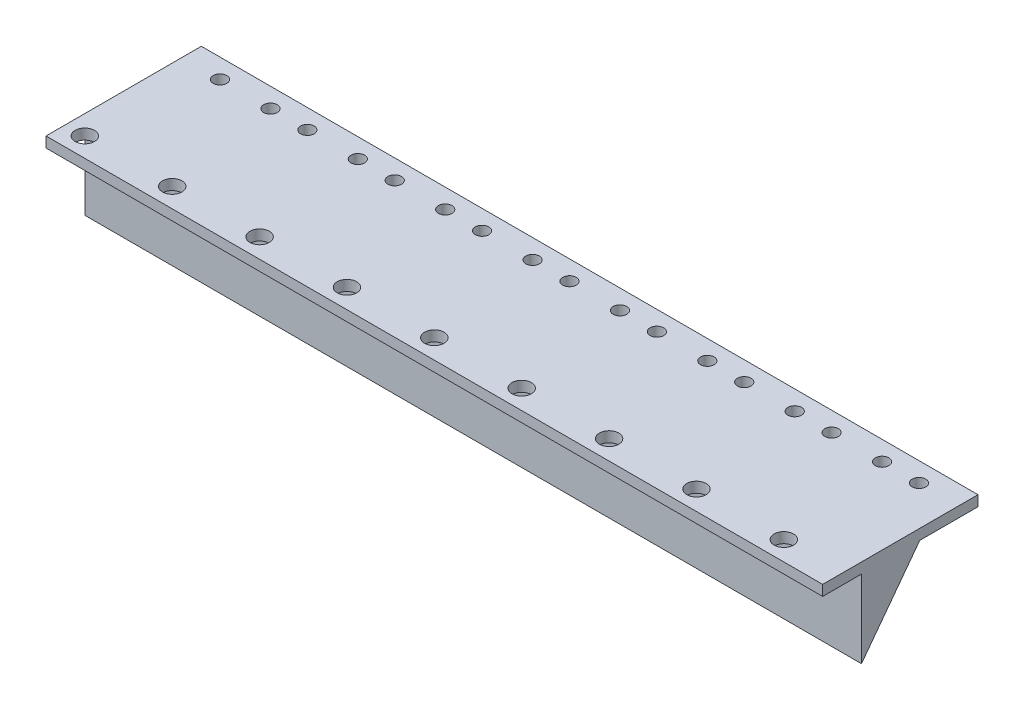
SolidWorks part; units mm, degrees
ref_plane "Front Plane" through (0, 0, 0) normal (0, 0, 1) x (1, 0, 0)
ref_plane "Top Plane" through (0, 0, 0) normal (0, 1, 0) x (1, 0, 0)
ref_plane "Right Plane" through (0, 0, 0) normal (1, 0, 0) x (0, 0, -1)
sketch "Sketch1" plane through (0, 0, 0) normal (0, 1, 0) x (1, 0, 0)
  line L1 (-100, -20) -> (100, -20)
  line L2 (-100, -20) -> (-100, 20)
  line L3 (-100, 20) -> (100, 20)
  line L4 (100, -20) -> (100, 20)
  line L5 (-100, -20) -> (100, 20) construction
  line L6 (-100, 20) -> (100, -20) construction
  point P0 (0, 0)
  dimension "D1" = 200
  dimension "D2" = 40
extrude "Boss-Extrude1" add sketch "Sketch1" along normal blind 2.7
sketch "Sketch2" plane through (0, 2.7, 0) normal (0, 1, 0) x (1, 0, 0)
  line L0 (100, 20) -> (-100, 20) construction
  line L1 (-100, 20) -> (-100, -20) construction
  circle A0 centre (-90.2, 15) radius 1.75
  dimension "D1" = 3.5
  dimension "D2" = 5
  dimension "D3" = 9.8
extrude "Cut-Extrude1" cut sketch "Sketch2" against normal through all contours A0
sketch "Sketch3" plane through (0, 2.7, 0) normal (0, 1, 0) x (1, 0, 0)
  line L0 (100, 20) -> (-100, 20) construction
  circle A0 centre (-77.2, 15) radius 1.75
  circle A1 centre (-90.2, 15) radius 1.75 construction
  dimension "D1" = 3.5
  dimension "D2" = 5
  dimension "D3" = 13
extrude "Cut-Extrude2" cut sketch "Sketch3" against normal through all
sketch "Sketch4" plane through (0, 2.7, 0) normal (0, 1, 0) x (1, 0, 0)
  line L0 (100, 20) -> (-100, 20) construction
  circle A0 centre (-67.7, 15) radius 1.75
  circle A1 centre (-77.2, 15) radius 1.75 construction
  dimension "D1" = 3.5
  dimension "D2" = 5
  dimension "D3" = 9.5
extrude "Cut-Extrude3" cut sketch "Sketch4" against normal through all
sketch "Sketch5" plane through (0, 2.7, 0) normal (0, 1, 0) x (1, 0, 0)
  line L0 (100, 20) -> (-100, 20) construction
  circle A0 centre (-54.7, 15) radius 1.75
  circle A1 centre (-67.7, 15) radius 1.75 construction
  dimension "D1" = 3.5
  dimension "D2" = 5
  dimension "D3" = 13
extrude "Cut-Extrude4" cut sketch "Sketch5" against normal through all
pattern_linear "LPattern2" count 2 spacing 9.5 along (1, 0, 0) of "Cut-Extrude4"
sketch "Sketch6" plane through (0, 2.7, 0) normal (0, 1, 0) x (1, 0, 0)
  line L1 (100, 20) -> (-100, 20) construction
  circle A0 centre (-32.2, 15) radius 1.75
  circle A2 centre (-45.2, 15) radius 1.75 construction
  circle A3 centre (-22.7, 15) radius 1.75
  dimension "D1" = 3.5
  dimension "D4" = 3.5
  dimension "D2" = 5
  dimension "D3" = 13
  dimension "D5" = 9.5
  dimension "D6" = 5
extrude "Cut-Extrude5" cut sketch "Sketch6" against normal through all
sketch "Sketch7" plane through (0, 2.7, 0) normal (0, 1, 0) x (1, 0, 0)
  line L0 (100, 20) -> (-100, 20) construction
  circle A0 centre (-9.7, 15) radius 1.75
  circle A1 centre (-22.7, 15) radius 1.75 construction
  circle A2 centre (-0.2, 15) radius 1.75
  circle A3 centre (12.8, 15) radius 1.75
  circle A4 centre (22.3, 15) radius 1.75
  circle A5 centre (35.3, 15) radius 1.75
  circle A6 centre (44.8, 15) radius 1.75
  circle A7 centre (57.8, 15) radius 1.75
  circle A8 centre (67.3, 15) radius 1.75
  circle A9 centre (80.3, 15) radius 1.75
  circle A10 centre (89.8, 15) radius 1.75
  dimension "D1" = 3.5
  dimension "D3" = 5
  dimension "D4" = 3.5
  dimension "D5" = 5
  dimension "D7" = 3.5
  dimension "D10" = 3.5
  dimension "D12" = 5
  dimension "D13" = 3.5
  dimension "D16" = 3.5
  dimension "D17" = 9.5
  dimension "D19" = 3.5
  dimension "D22" = 3.5
  dimension "D24" = 9.5
  dimension "D25" = 3.5
  dimension "D28" = 3.5
  dimension "D2" = 13
  dimension "D6" = 9.5
  dimension "D8" = 5
  dimension "D9" = 13
  dimension "D11" = 9.5
  dimension "D14" = 5
  dimension "D15" = 13
  dimension "D18" = 5
  dimension "D20" = 5
  dimension "D21" = 13
  dimension "D23" = 5
  dimension "D26" = 13
  dimension "D27" = 5
  dimension "D29" = 5
  dimension "D30" = 9.5
extrude "Cut-Extrude6" cut sketch "Sketch7" against normal through all
sketch "Sketch8" plane through (0, 2.7, 0) normal (0, 1, 0) x (1, 0, 0)
  line L0 (-100, -20) -> (100, -20) construction
  line L1 (-100, 20) -> (-100, -20) construction
  circle A0 centre (-95, -15) radius 2.5
  dimension "D1" = 5
  dimension "D2" = 5
  dimension "D3" = 5
extrude "Cut-Extrude7" cut sketch "Sketch8" against normal through all
pattern_linear "LPattern3" count 9 spacing 22.5 along (1, 0, 0) of "Cut-Extrude7"
ref_plane "Plane1" through (100, 0, 0) normal (1, 0, 0) x (0, 0, -1)
ref_plane "Plane2" through (-100, 0, 0) normal (-1, 0, 0) x (0, 0, 1)
sketch "Sketch10" plane through (100, 0, 0) normal (1, 0, 0) x (0, 0, -1)
  line L0 (-10, 0) -> (-10, -20)
  line L1 (-20, 0) -> (20, 0) construction
  line L2 (-10, -20) -> (5, 0)
  line L3 (5, 0) -> (-10, 0)
  line L5 (20, 2.7) -> (20, 0) construction
  dimension "D1" = 20
  dimension "D2" = 15
  dimension "D3" = 15
extrude "Boss-Extrude2" add sketch "Sketch10" against normal blind 200
